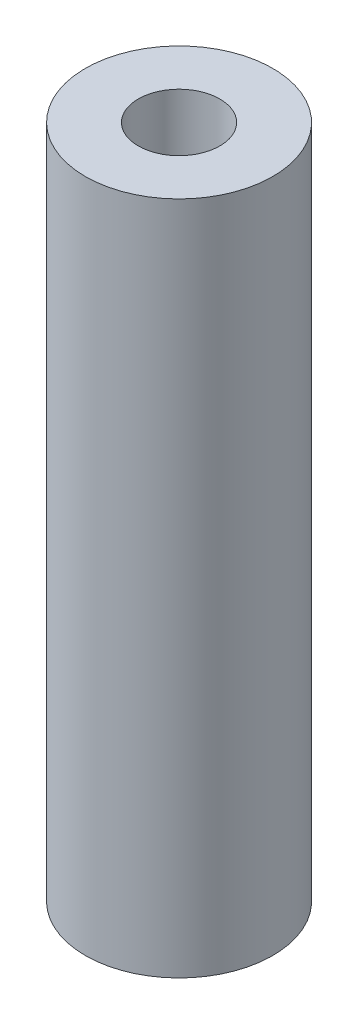
SolidWorks part; units mm, degrees
ref_plane "Alzado" through (0, 0, 0) normal (0, 0, 1) x (1, 0, 0)
ref_plane "Planta" through (0, 0, 0) normal (0, 1, 0) x (1, 0, 0)
ref_plane "Vista lateral" through (0, 0, 0) normal (1, 0, 0) x (0, 0, -1)
sketch "Croquis1" plane through (0, 0, 0) normal (0, 1, 0) x (1, 0, 0)
  circle A0 centre (0, 0) radius 5
  dimension "D1" = 10
extrude "Saliente-Extruir1" add sketch "Croquis1" along normal blind 36
sketch "Croquis2" plane through (0, 36, 0) normal (0, 1, 0) x (1, 0, 0)
  circle A0 centre (0, 0) radius 2.175
  dimension "D1" = 4.35
extrude "Cortar-Extruir1" cut sketch "Croquis2" against normal up to surface (36 mm away) up to face at (0, 0, 5)
